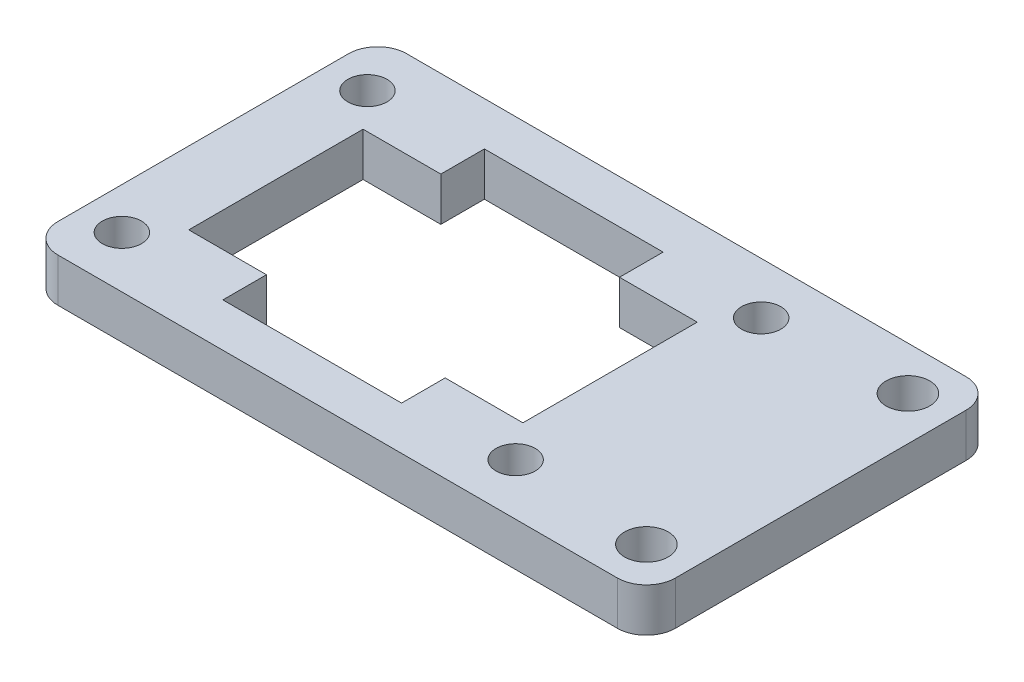
SolidWorks part; units mm, degrees
ref_plane "Front Plane" through (0, 0, 0) normal (0, 0, 1) x (1, 0, 0)
ref_plane "Top Plane" through (0, 0, 0) normal (0, 1, 0) x (1, 0, 0)
ref_plane "Right Plane" through (0, 0, 0) normal (1, 0, 0) x (0, 0, -1)
sketch "Sketch1" plane through (0, 0, 0) normal (0, 1, 0) x (1, 0, 0)
  line L0 (16.5, 21) -> (16.5, 18) construction
  line L1 (0, 0) -> (42.5, 0)
  line L2 (0, 0) -> (0, 24)
  line L3 (0, 24) -> (42.5, 24)
  line L4 (42.5, 0) -> (42.5, 24)
  line L5 (5, 18) -> (28, 18)
  line L6 (5, 18) -> (5, 6)
  line L7 (5, 6) -> (28, 6)
  line L8 (28, 18) -> (28, 6)
  line L9 (10.5, 18) -> (22.5, 18)
  line L10 (10.5, 18) -> (10.5, 21)
  line L11 (10.5, 21) -> (22.5, 21)
  line L12 (22.5, 18) -> (22.5, 21)
  line L13 (10.5, 6) -> (22.5, 6)
  line L14 (10.5, 6) -> (10.5, 3)
  line L15 (10.5, 3) -> (22.5, 3)
  line L16 (22.5, 6) -> (22.5, 3)
  circle A0 centre (2.85, 20.45) radius 1.35
  circle A1 centre (2.85, 3.55) radius 1.35
  circle A2 centre (29.95, 20.45) radius 1.35
  circle A3 centre (29.95, 3.55) radius 1.35
  circle A4 centre (39.5, 3) radius 1.5
  circle A5 centre (39.5, 21) radius 1.5
  point P29 (39.3154, 3.053)
  point P30 (0, 0)
  dimension "D9" = 3
  dimension "D10" = 2.7
  dimension "D11" = 2.7
  dimension "D1" = 42.5
  dimension "D2" = 24
  dimension "D3" = 5
  dimension "D4" = 5.5
  dimension "D5" = 18
  dimension "D6" = 23
  dimension "D7" = 3
  dimension "D8" = 12
  dimension "D12" = 3
  dimension "D13" = 3.55
  dimension "D14" = 3.55
  dimension "D15" = 2.85
  dimension "D16" = 12.55
  dimension "D17" = 3
  dimension "D18" = 3
extrude "Boss-Extrude1" add sketch "Sketch1" along normal blind 3 contours L1 L4 L3 L2 A5 A4 A3 A2 A1 A0 L7 L16 L15 L14 L6 L5 L10 L11 L12 L8
sketch "Sketch2" plane through (0, 3, 0) normal (0, 1, 0) x (1, 0, 0)
  line L0 (10.5, 3) -> (22.5, 3) construction
  line L1 (22.5, 6) -> (22.65, 6)
  line L2 (22.5, 6) -> (22.5, 3)
  line L3 (22.5, 3) -> (22.65, 3)
  line L4 (22.65, 6) -> (22.65, 3)
  line L5 (10.5, 6) -> (10.35, 6)
  line L6 (10.5, 6) -> (10.5, 3)
  line L7 (10.5, 3) -> (10.35, 3)
  line L8 (10.35, 6) -> (10.35, 3)
  line L9 (10.5, 21) -> (22.5, 21) construction
  line L10 (22.5, 18) -> (22.65, 18)
  line L11 (22.5, 18) -> (22.5, 21)
  line L12 (22.5, 21) -> (22.65, 21)
  line L13 (22.65, 18) -> (22.65, 21)
  line L14 (10.5, 18) -> (10.35, 18)
  line L15 (10.5, 18) -> (10.5, 21)
  line L16 (10.5, 21) -> (10.35, 21)
  line L17 (10.35, 18) -> (10.35, 21)
  dimension "D1" = 0.15
extrude "Cut-Extrude1" cut sketch "Sketch2" against normal through all
fillet "Fillet1" radius 2 4 edges at (0, 1.5, -24) (42.5, 1.5, -24) (42.5, 1.5, 0) (0, 1.5, 0)
